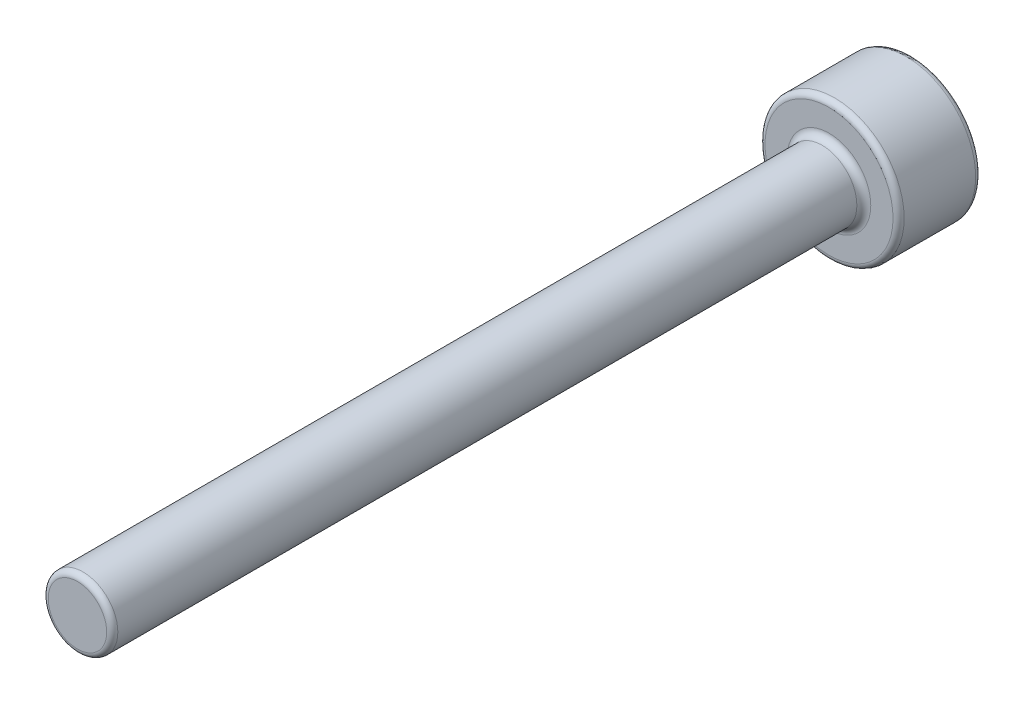
SolidWorks part; units mm, degrees
material "合金鋼"
ref_plane "前基準面" through (0, 0, 0) normal (0, 0, 1) x (1, 0, 0)
ref_plane "上基準面" through (0, 0, 0) normal (0, 1, 0) x (1, 0, 0)
ref_plane "右基準面" through (0, 0, 0) normal (1, 0, 0) x (0, 0, -1)
sketch "草圖1" plane through (0, 0, 0) normal (0, 0, 1) x (1, 0, 0)
  circle A0 centre (0, 0) radius 5
  dimension "螺絲頭外徑" = 10
extrude "螺釘頭" add sketch "草圖1" along normal blind 6
sketch "草圖2" plane through (0, 0, 6) normal (0, 0, 1) x (1, 0, 0)
  circle A0 centre (0, 0) radius 2.5
  dimension "螺紋部外徑" = 5
extrude "螺釘部" add sketch "草圖2" along normal blind 54
sketch "草圖3" plane through (0, 0, 0) normal (0, 0, -1) x (-1, 0, 0)
  line L1 (2.5, -1.4434) -> (2.5, 1.4434)
  line L2 (2.5, 1.4434) -> (0, 2.8868)
  line L3 (0, 2.8868) -> (-2.5, 1.4434)
  line L4 (-2.5, 1.4434) -> (-2.5, -1.4434)
  line L5 (-2.5, -1.4434) -> (0, -2.8868)
  line L6 (0, -2.8868) -> (2.5, -1.4434)
  circle A0 centre (0, 0) radius 2.5 construction
  dimension "六角洞直徑" = 5
extrude "內六角孔" cut sketch "草圖3" against normal blind 3
chamfer "頭部導角" distance 0.4 angle 30 1 edges at (5, 0, 0)
fillet "頸部圓角" radius 0.5 1 edges at (2.5, 0, 6)
sketch "長度中間點" plane through (0, 0, 0) normal (1, 0, 0) x (0, 0, -1)
  line L1 (-60, 4.25) -> (0, 4.25) construction
  line L2 (-60, 2.5) -> (-60, -2.5) construction
  line L3 (0, -4.6) -> (0, 4.6) construction
  point P0 (-30, 4.25)
ref_plane "長度中間面" through (0, 0, 30) normal (0, 0, 1) x (1, 0, 0)
fillet "圓角1" [suppressed] radius 6
fillet "圓角2" radius 0.4 16 edges at (5, 0, 6) (5, 0, 0.2309) (-1.25, 2.1651, 0) (1.25, 2.1651, 0) (2.5, 0, 0) (1.25, -2.1651, 0) (-1.25, -2.1651, 0) (-2.5, 0, 0) (4.6, 0, 0) (2.5, 0, 60) (1.25, -2.1651, 3) (2.5, 0, 3) (1.25, 2.1651, 3) (-1.25, 2.1651, 3) (-2.5, 0, 3) (-1.25, -2.1651, 3)
sketch "Sketch1" plane through (0, 0, 0) normal (0, 1, 0) x (1, 0, 0)
  circle A0 centre (0, 0) radius 3
  dimension "D1" = 6
extrude "止付_螺紋部" [suppressed] add sketch "Sketch1" against normal blind 20
sketch "Sketch2" [suppressed] plane through (0, 0, 0) normal (0, 1, 0) x (1, 0, 0)
  line L1 (0.866, -1.5) -> (1.7321, 0)
  line L2 (1.7321, 0) -> (0.866, 1.5)
  line L3 (0.866, 1.5) -> (-0.866, 1.5)
  line L4 (-0.866, 1.5) -> (-1.7321, 0)
  line L5 (-1.7321, 0) -> (-0.866, -1.5)
  line L6 (-0.866, -1.5) -> (0.866, -1.5)
  circle A0 centre (0, 0) radius 1.5 construction
  dimension "D1" = 3
extrude "止付_六角孔" [suppressed] cut sketch "Sketch2" against normal blind 2
chamfer "止付_邊導角" [suppressed] distance 0.3
sketch "Sketch3" plane through (0, 0, 0) normal (0, 1, 0) x (1, 0, 0)
  circle A0 centre (0, 0) radius 5
  dimension "D1" = 10
extrude "薄頭_頭部" [suppressed] add sketch "Sketch3" along normal blind 1.5
sketch "Sketch4" [suppressed] plane through (0, 1.5, 0) normal (0, 1, 0) x (1, 0, 0)
  line L1 (0.2887, -0.5) -> (0.5774, 0)
  line L2 (0.5774, 0) -> (0.2887, 0.5)
  line L3 (0.2887, 0.5) -> (-0.2887, 0.5)
  line L4 (-0.2887, 0.5) -> (-0.5774, 0)
  line L5 (-0.5774, 0) -> (-0.2887, -0.5)
  line L6 (-0.2887, -0.5) -> (0.2887, -0.5)
  circle A0 centre (0, 0) radius 0.5 construction
  dimension "D1" = 1
extrude "薄頭_六角孔" [suppressed] cut sketch "Sketch4" against normal blind 1
sketch "Sketch5" [suppressed] plane through (0, 0, 0) normal (0, -1, 0) x (1, 0, 0)
  circle A0 centre (0, 0) radius 3
  dimension "D1" = 6
extrude "薄頭_螺紋部" [suppressed] add sketch "Sketch5" along normal blind 16
fillet "薄頭_導圓" [suppressed] radius 0.5
